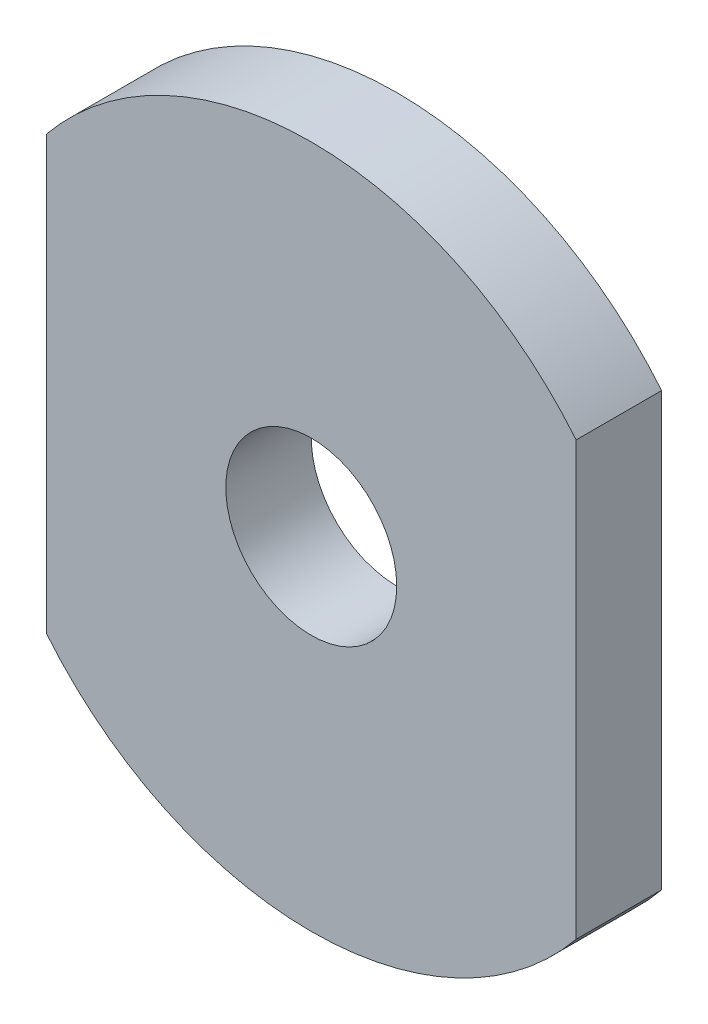
SolidWorks part; units mm, degrees
ref_plane "Front Plane" through (0, 0, 0) normal (0, 0, 1) x (1, 0, 0)
ref_plane "Top Plane" through (0, 0, 0) normal (0, 1, 0) x (1, 0, 0)
ref_plane "Right Plane" through (0, 0, 0) normal (1, 0, 0) x (0, 0, -1)
sketch "Sketch1" plane through (0, 0, 0) normal (0, 0, 1) x (1, 0, 0)
  line L0 (-15.4928, 12.6481) -> (-15.4928, -12.6481)
  line L1 (15.4928, 12.6481) -> (15.4928, -12.6481)
  circle A0 centre (0, 0) radius 5
  arc A1 (-15.4928, -12.6481) -> (15.4928, -12.6481) centre (0, 0) ccw
  arc A2 (15.4928, 12.6481) -> (-15.4928, 12.6481) centre (0, 0) ccw
  dimension "D1" = 10
  dimension "D2" = 40
  dimension "D3" = 25.2962
extrude "Boss-Extrude1" add sketch "Sketch1" along normal blind 5
